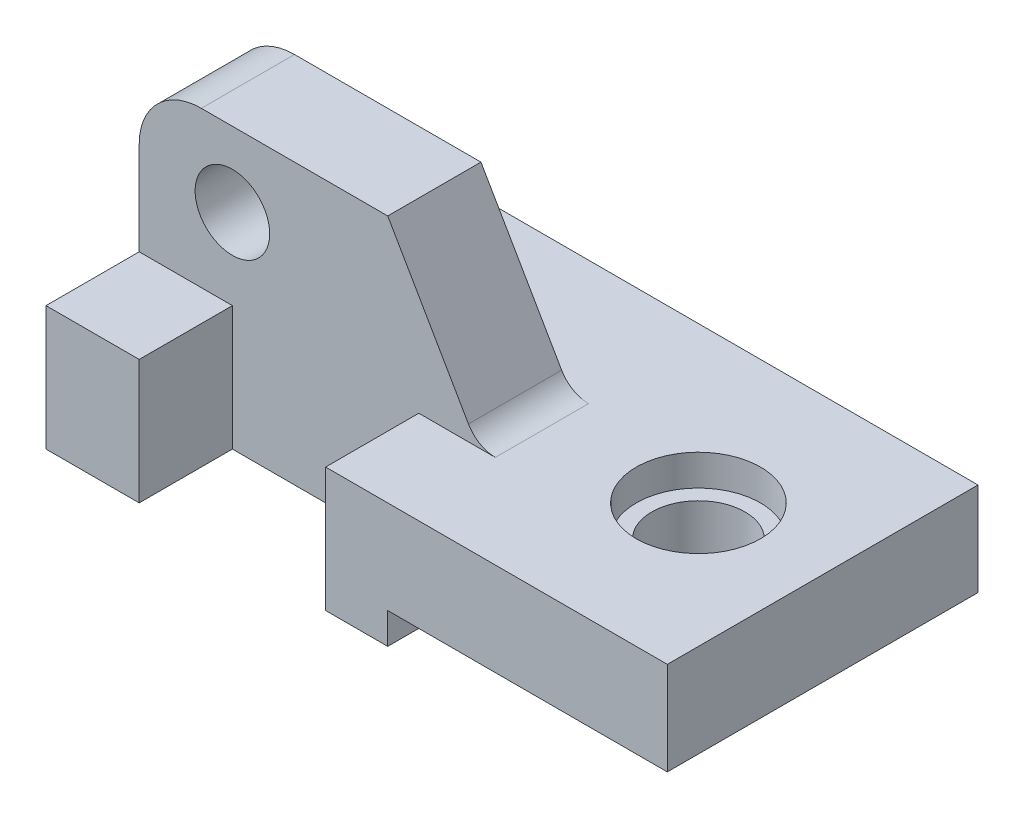
SolidWorks part; units mm, degrees
ref_plane "Front Plane" through (0, 0, 0) normal (0, 0, 1) x (1, 0, 0)
ref_plane "Top Plane" through (0, 0, 0) normal (0, 1, 0) x (1, 0, 0)
ref_plane "Right Plane" through (0, 0, 0) normal (1, 0, 0) x (0, 0, -1)
sketch "Sketch2" plane through (0, 0, 0) normal (0, 0, 1) x (1, 0, 0)
  line L0 (0, 0) -> (55, 0)
  line L1 (55, 0) -> (55, 5)
  line L2 (55, 5) -> (100, 5)
  line L3 (100, 5) -> (100, 20)
  line L4 (100, 20) -> (0, 20)
  line L5 (0, 20) -> (0, 0)
  line L6 (15, 20) -> (15, 0)
  line L7 (45, 20) -> (45, 0)
  dimension "D1" = 100
  dimension "D2" = 45
  dimension "D3" = 15
  dimension "D4" = 45
  dimension "D5" = 15
  dimension "D6" = 20
extrude "Boss-Extrude1" add sketch "Sketch2" along normal blind 15 contours L6 L4 L5 L0 | L4 L7 L0 L1 L2 L3
sketch "Sketch3" plane through (0, 0, 0) normal (0, 0, 1) x (1, 0, 0)
  line L0 (100, 20) -> (100, 5)
  line L1 (100, 5) -> (55, 5)
  line L2 (55, 5) -> (100, 5) construction
  line L3 (55, 5) -> (55, 0)
  line L4 (55, 0) -> (0, 0)
  line L5 (0, 0) -> (0, 20)
  line L6 (0, 20) -> (100, 20)
extrude "Boss-Extrude2" add sketch "Sketch3" against normal blind 35
sketch "Sketch9" plane through (0, 0, 0) normal (0, 0, 1) x (1, 0, 0)
  line L3 (40, 45) -> (10, 45)
  line L4 (0, 35) -> (0, 20)
  line L5 (0, 20) -> (57.3205, 20)
  line L7 (100, 20) -> (45, 20) construction
  line L8 (40, 45) -> (52.9904, 22.5)
  arc A0 (10, 45) -> (0, 35) centre (10, 35) ccw
  arc A1 (52.9904, 22.5) -> (57.3205, 20) centre (57.3205, 25) ccw
  circle A2 centre (15, 33) radius 6
  point P4 (0, 45)
  dimension "D4" = 10
  dimension "D5" = 10
  dimension "D6" = 12
  dimension "D1" = 40
  dimension "D2" = 25
  dimension "D3" = 120
  dimension "D7" = 15
  dimension "D8" = 12
extrude "Boss-Extrude6" add sketch "Sketch9" against normal blind 15
hole_wizard "Hole1" positions "Sketch13" profile "Sketch12" legacy
sketch "Sketch13" plane through (0, 20, 0) normal (0, 1, 0) x (1, 0, 0)
  point P0 (80, 10)
  dimension "D1" = 25
  dimension "D2" = 20
sketch "Sketch12" plane through (80, 20, -10) normal (1, 0, 0) x (0, 0, 1)
  line L0 (0, 0) -> (0, 99.9687)
  line L1 (0, 99.9687) -> (7.5, 99.9687)
  line L2 (7.5, 99.9687) -> (7.5, 5)
  line L3 (7.5, 5) -> (10, 5)
  line L4 (10, 5) -> (10, 0)
  line L5 (10, 0) -> (0, 0)
  line L6 (0, 110) -> (0, -10) construction
  dimension "Diameter" = 15
  dimension "Depth" = 100
  dimension "C-Bore Diameter" = 20
  dimension "C-Bore Depth" = 5
